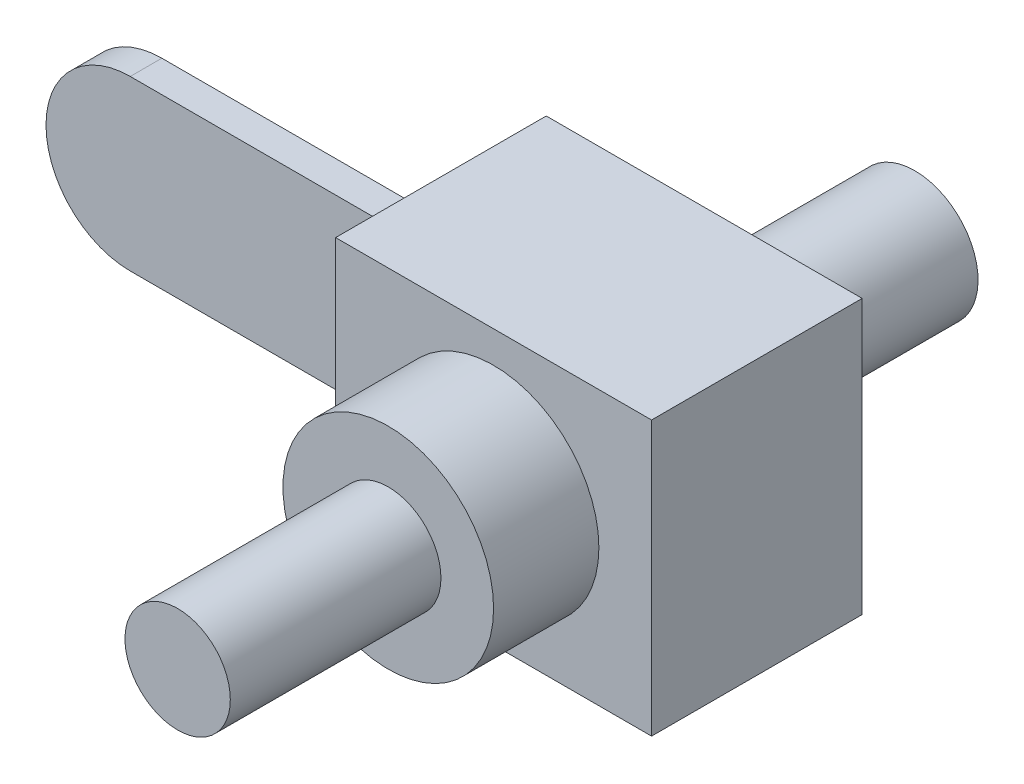
SolidWorks part; units mm, degrees
ref_plane "Front Plane" through (0, 0, 0) normal (0, 0, 1) x (1, 0, 0)
ref_plane "Top Plane" through (0, 0, 0) normal (0, 1, 0) x (1, 0, 0)
ref_plane "Right Plane" through (0, 0, 0) normal (1, 0, 0) x (0, 0, -1)
sketch "Sketch1" plane through (0, 0, 0) normal (0, 0, 1) x (1, 0, 0)
  line L0 (0, 40) -> (140, 40)
  line L1 (140, 40) -> (140, -40)
  line L2 (140, -40) -> (0, -40)
  arc A0 (0, 40) -> (0, -40) centre (0, 0) ccw
  dimension "D1" = 80
  dimension "180" = 140
extrude "Boss-Extrude1" add sketch "Sketch1" along normal mid plane 15
sketch "Sketch3" plane through (140, 0, 0) normal (1, 0, 0) x (0, 0, -1)
  line L1 (-50, 65) -> (50, 65)
  line L2 (-50, 65) -> (-50, -65)
  line L3 (-50, -65) -> (50, -65)
  line L4 (50, 65) -> (50, -65)
  line L5 (-50, 65) -> (50, -65) construction
  line L6 (-50, -65) -> (50, 65) construction
  point P0 (0, 0)
  dimension "D1" = 100
  dimension "D2" = 130
extrude "Boss-Extrude2" add sketch "Sketch3" along normal blind 150
sketch "Sketch4" plane through (0, 0, -50) normal (0, 0, -1) x (-1, 0, 0)
  line L0 (-290, 65) -> (-140, 65) construction
  circle A0 centre (-215, 0) radius 30
  point P5 (-215, 65)
  dimension "D1" = 60
extrude "Boss-Extrude3" add sketch "Sketch4" along normal blind 100
sketch "Sketch5" plane through (0, 0, 50) normal (0, 0, 1) x (1, 0, 0)
  line L0 (290, -65) -> (140, -65) construction
  circle A0 centre (215, 0) radius 50
  point P5 (215, -65)
  dimension "D1" = 100
extrude "Boss-Extrude4" add sketch "Sketch5" along normal blind 50
sketch "Sketch6" plane through (0, 0, 100) normal (0, 0, 1) x (1, 0, 0)
  circle A0 centre (215, 0) radius 25
extrude "Boss-Extrude5" add sketch "Sketch6" along normal blind 100
sketch "Sketch7" plane through (0, 0, 200) normal (0, 0, 1) x (1, 0, 0)
  circle A0 centre (215, 0) radius 55
  dimension "D1" = 110
sketch "Sketch8" plane through (0, 0, -7.5) normal (0, 0, -1) x (-1, 0, 0)
  point P0 (0, 0)
